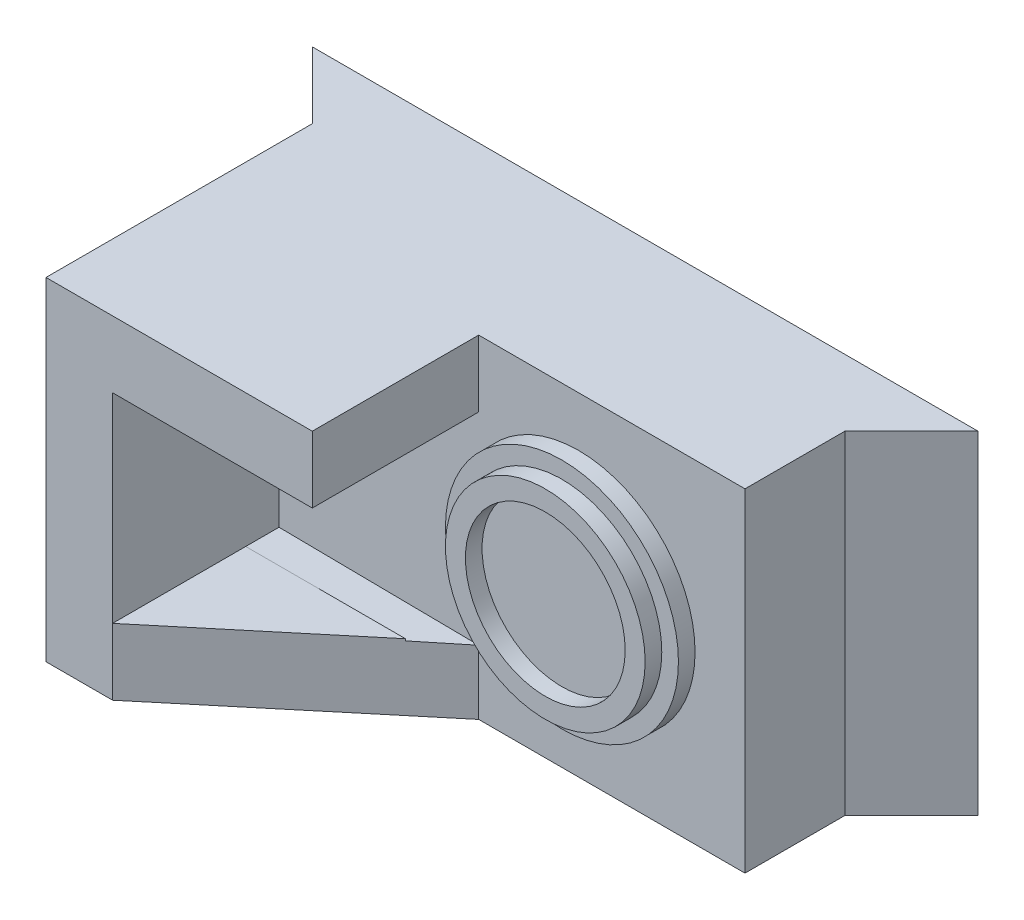
SolidWorks part; units mm, degrees
ref_plane "Plan de face" through (0, 0, 0) normal (0, 0, 1) x (1, 0, 0)
ref_plane "Plan de dessus" through (0, 0, 0) normal (0, 1, 0) x (1, 0, 0)
ref_plane "Plan de droite" through (0, 0, 0) normal (1, 0, 0) x (0, 0, -1)
sketch "Esquisse2" plane through (0, 0, 0) normal (0, 0, 1) x (1, 0, 0)
  line L1 (-30.1084, 18.8854) -> (69.8916, 18.8854)
  line L2 (-30.1084, 18.8854) -> (-30.1084, -31.1146)
  line L3 (-30.1084, -31.1146) -> (69.8916, -31.1146)
  line L4 (69.8916, 18.8854) -> (69.8916, -31.1146)
  dimension "D1" = 50
  dimension "D2" = 100
extrude "Boss.-Extru.1" add sketch "Esquisse2" along normal blind 50
sketch "Esquisse5" plane through (0, -31.1146, 0) normal (0, -1, 0) x (-1, 0, 0)
  line L3 (30.1084, 0) -> (20.1084, -10)
  line L4 (20.1084, -10) -> (20.1084, -50)
  line L5 (30.1084, -50) -> (-69.8916, -50) construction
  line L6 (20.1084, -50) -> (30.1084, -50)
  line L7 (30.1084, -50) -> (30.1084, 0)
  line L8 (-69.8916, 0) -> (-59.8916, -10)
  line L9 (-59.8916, -10) -> (-59.8916, -50)
  line L10 (-59.8916, -50) -> (-69.8916, -50)
  line L11 (-69.8916, -50) -> (-69.8916, 0)
  point P0 (20.1084, -10)
  point P1 (20.1084, -10)
  point P2 (20.1084, -10)
  point P3 (-59.8916, -10)
extrude "Enlèv. mat.-Extru.2" cut sketch "Esquisse5" against normal through all
sketch "Esquisse7" plane through (0, 0, 50) normal (0, 0, 1) x (1, 0, 0)
  line L2 (-20.1084, -31.1146) -> (59.8916, -31.1146) construction
  line L3 (19.8916, -31.1146) -> (59.8916, -31.1146)
  line L4 (19.8916, -31.1146) -> (19.8916, 18.8854)
  line L5 (19.8916, 18.8854) -> (59.8916, 18.8854)
  line L6 (59.8916, -31.1146) -> (59.8916, 18.8854)
  line L7 (59.8916, 18.8854) -> (59.8916, -31.1146) construction
  line L8 (59.8916, 18.8854) -> (-20.1084, 18.8854) construction
  point P1 (19.8916, -30.5344)
extrude "Enlèv. mat.-Extru.3" cut sketch "Esquisse7" against normal blind 20
sketch "Esquisse8" plane through (0, 0, 50) normal (0, 0, 1) x (1, 0, 0)
  line L4 (19.8916, 18.8854) -> (19.8916, -31.1146) construction
  line L5 (-10.1084, 8.8854) -> (19.8916, 8.8854)
  line L6 (-10.1084, 8.8854) -> (-10.1084, -21.1146)
  line L7 (-10.1084, -21.1146) -> (19.8916, -21.1146)
  line L8 (19.8916, 8.8854) -> (19.8916, -21.1146)
  point P0 (-10.1084, 8.8854)
  point P1 (-10.1084, -21.1146)
extrude "Enlèv. mat.-Extru.4" cut sketch "Esquisse8" against normal blind 20
sketch "Esquisse9" plane through (0, 0, 30) normal (0, 0, 1) x (1, 0, 0)
  line L2 (19.8916, 18.8854) -> (19.8916, 8.8854)
  line L3 (19.8916, 8.8854) -> (-10.1084, 8.8854)
  line L4 (-10.1084, 8.8854) -> (-10.1084, -20.2656)
  line L5 (-10.1084, 8.8854) -> (-10.1084, -21.1146) construction
  line L6 (-10.1084, -20.2656) -> (-10.1084, -21.1146)
  line L7 (-10.1084, -21.1146) -> (19.8916, -21.1146)
  line L8 (19.8916, -21.1146) -> (19.8916, -31.1146)
  line L9 (19.8916, -31.1146) -> (19.8916, -21.1146)
  line L10 (19.8916, -21.1146) -> (26.6284, -21.5408)
  line L11 (19.8916, 8.8854) -> (25.8778, 8.8854)
  circle A2 centre (34.8916, -6.1146) radius 17.5
  point P0 (34.8916, -6.1146)
  line M5 (19.8916, 8.8854) -> (-10.1084, 8.8854)
  line M6 (-10.1084, 8.8854) -> (-10.1084, -21.1146)
  line M7 (-10.1084, -21.1146) -> (19.8916, -21.1146)
extrude "Enlèv. mat.-Extru.7" cut sketch "Esquisse9" against normal blind 2.5 contours A2 L11 L10 M5 M6 M7
sketch "Esquisse11" plane through (0, 0, 30) normal (0, 0, 1) x (1, 0, 0)
  line L0 (19.8916, -21.1146) -> (25.8778, -21.1146)
  line L2 (25.8778, 8.8854) -> (19.8916, 8.8854)
  line L3 (-10.1084, 8.8854) -> (25.8778, 8.8854) construction
  line L4 (19.8916, 8.8854) -> (25.8778, 8.8854) construction
  line L5 (19.8916, 8.8854) -> (19.8916, 18.8854)
  line L6 (19.8916, 18.8854) -> (59.8916, 18.8854)
  line L7 (59.8916, 18.8854) -> (59.8916, -31.1146)
  line L8 (59.8916, -31.1146) -> (19.8916, -31.1146)
  line L9 (19.8916, -31.1146) -> (19.8916, -21.1146)
  circle A0 centre (34.8916, -6.1146) radius 17.5
  line M2 (26.6284, -21.5408) -> (19.8916, -21.1146)
  line M3 (19.8916, -21.1146) -> (19.8916, -31.1146)
  line M4 (19.8916, -31.1146) -> (59.8916, -31.1146)
  line M5 (59.8916, -31.1146) -> (59.8916, 18.8854)
  line M6 (59.8916, 18.8854) -> (19.8916, 18.8854)
  line M7 (19.8916, 18.8854) -> (19.8916, 8.8854)
  line M8 (19.8916, 8.8854) -> (25.8778, 8.8854)
extrude "Enlèv. mat.-Extru.10" cut sketch "Esquisse11" against normal blind 5 contours A0 M2 M3 M4 M5 M6 M7 M8
sketch "Esquisse13" plane through (0, 0, 30) normal (0, 0, 1) x (1, 0, 0)
  line L2 (25.8778, 8.8854) -> (-10.1084, 8.8854)
  line L3 (19.8916, 8.8854) -> (25.8778, 8.8854) construction
  line L4 (-10.1084, 8.8854) -> (-10.1084, -21.1146)
  line L5 (-10.1084, -21.1146) -> (26.6284, -21.5408)
  circle A0 centre (34.8916, -6.1146) radius 17.5
  circle M1 centre (34.8916, -6.1146) radius 17.5
extrude "Enlèv. mat.-Extru.11" cut sketch "Esquisse13" against normal blind 5 contours L4 L5 L2 M1
sketch "Esquisse15" plane through (0, -31.1146, 0) normal (0, -1, 0) x (-1, 0, 0)
  line L0 (20.1084, -50) -> (-19.8916, -50) construction
  line L1 (10.1084, -50) -> (-19.8916, -25)
  line L2 (-19.8916, -25) -> (-19.8916, -50)
  line L3 (-19.8916, -50) -> (10.1084, -50)
  point P0 (10.1084, -50)
extrude "Enlèv. mat.-Extru.12" cut sketch "Esquisse15" against normal blind 10
sketch "Esquisse16" plane through (0, 0, 30) normal (0, 0, 1) x (1, 0, 0)
  circle A0 centre (34.8916, -6.1146) radius 15
  circle A1 centre (34.8916, -6.1146) radius 17.5
  point P0 (34.8916, -6.1146)
extrude "Enlèv. mat.-Extru.13" cut sketch "Esquisse16" against normal blind 2.5
sketch "Esquisse17" plane through (0, 0, 30) normal (0, 0, 1) x (1, 0, 0)
  circle A0 centre (34.8916, -6.1146) radius 12
  point P0 (34.8916, -6.1146)
extrude "Enlèv. mat.-Extru.14" cut sketch "Esquisse17" against normal blind 2.5
